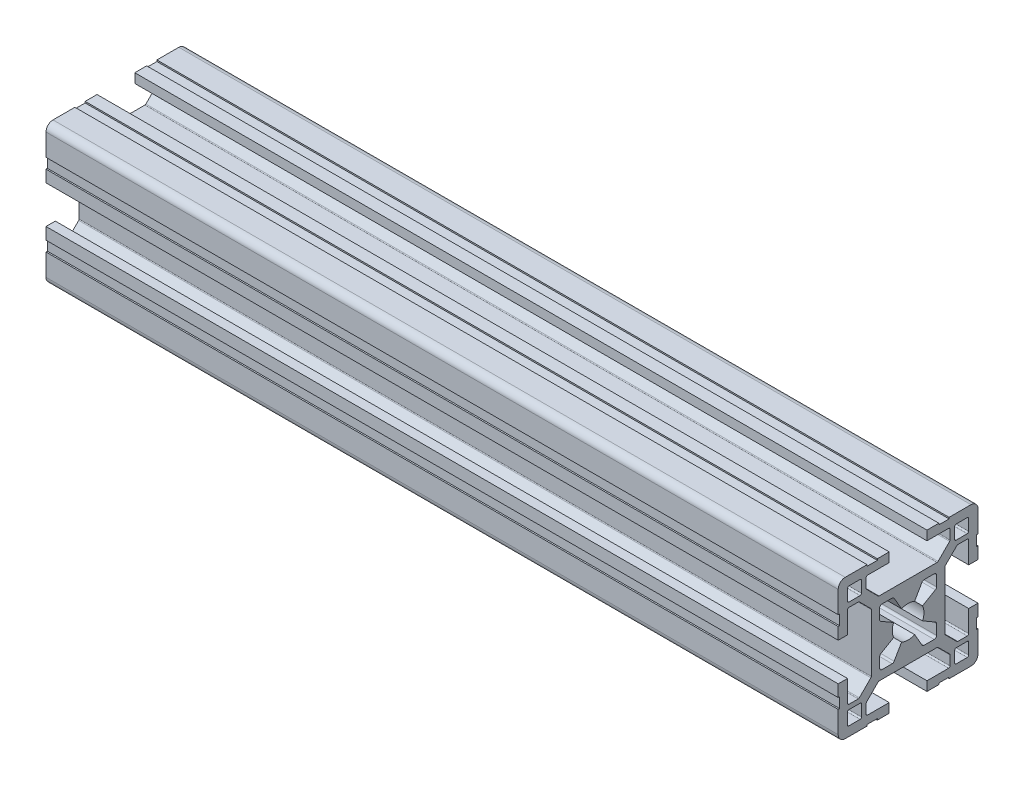
SolidWorks part; units mm, degrees
material "6063-T5"
ref_plane "Plano frontal" through (0, 0, 0) normal (0, 0, 1) x (1, 0, 0)
ref_plane "Plano superior" through (0, 0, 0) normal (0, 1, 0) x (1, 0, 0)
ref_plane "Plano direito" through (0, 0, 0) normal (1, 0, 0) x (0, 0, -1)
sketch "Esboço1" plane through (0, 0, 0) normal (0, 0, 1) x (1, 0, 0)
  line L0 (0, 0) -> (170, 0)
  dimension "D1" = 170
other "Quadrado PF30-11 - PERFIL 3030 CENTRO M8(1)"
ref_plane "Plano1" through (0, 0, 0) normal (1, 0, 0) x (0, 1, 0)
sketch "Sketch1" plane through (0, 0, 0) normal (1, 0, 0) x (0, 1, 0)
  line L0 (-6.1, -3.4254) -> (-6.1, -5.6)
  line L1 (-5.6, -6.1) -> (-3.4254, -6.1)
  line L2 (3.4254, -6.1) -> (5.6, -6.1)
  line L3 (6.1, -5.6) -> (6.1, -3.4254)
  line L4 (6.1, 3.4254) -> (6.1, 5.6)
  line L5 (5.6, 6.1) -> (3.4254, 6.1)
  line L6 (-3.4254, 6.1) -> (-5.6, 6.1)
  line L7 (-6.1, 5.6) -> (-6.1, 3.4254)
  line L8 (15, 6.6) -> (14.7, 6.6)
  line L9 (5.85, -2.9924) -> (3.097, -1.403)
  line L10 (10, 12.7) -> (10, 10.3)
  line L11 (13, -12.7) -> (13, -10.3)
  line L12 (-10.3, -10) -> (-12.7, -10)
  line L13 (-13, 12.7) -> (-13, 10.3)
  line L14 (3.097, 1.403) -> (5.85, 2.9924)
  line L15 (2.9924, 5.85) -> (1.403, 3.097)
  line L16 (-1.403, 3.097) -> (-2.9924, 5.85)
  line L17 (-5.85, 2.9924) -> (-3.097, 1.403)
  line L18 (-3.097, -1.403) -> (-5.85, -2.9924)
  line L19 (-2.9924, -5.85) -> (-1.403, -3.097)
  line L20 (1.403, -3.097) -> (2.9924, -5.85)
  line L21 (10.3, 10) -> (12.7, 10)
  line L22 (13, 10.3) -> (13, 12.7)
  line L23 (12.7, 13) -> (10.3, 13)
  line L24 (12.7, -10) -> (10.3, -10)
  line L25 (10, -10.3) -> (10, -12.7)
  line L26 (10.3, -13) -> (12.7, -13)
  line L27 (-13, -10.3) -> (-13, -12.7)
  line L28 (-12.7, -13) -> (-10.3, -13)
  line L29 (-10, -12.7) -> (-10, -10.3)
  line L30 (-12.7, 10) -> (-10.3, 10)
  line L31 (-10, 10.3) -> (-10, 12.7)
  line L32 (-10.3, 13) -> (-12.7, 13)
  line L33 (15, 4.05) -> (15, 6.6)
  line L34 (13, 4.05) -> (15, 4.05)
  line L35 (13, 8.7) -> (13, 4.05)
  line L36 (10.6799, 9) -> (12.7, 9)
  line L37 (7.9879, 6.4322) -> (10.4678, 8.9121)
  line L38 (7.9, -6.2201) -> (7.9, 6.2201)
  line L39 (10.4678, -8.9121) -> (7.9879, -6.4322)
  line L40 (12.7, -9) -> (10.6799, -9)
  line L41 (13, -4.05) -> (13, -8.7)
  line L42 (15, -4.05) -> (13, -4.05)
  line L43 (15, -6.6) -> (15, -4.05)
  line L44 (14.7, -6.6) -> (15, -6.6)
  line L45 (14.7, -8.8) -> (14.7, -6.6)
  line L46 (15, -8.8) -> (14.7, -8.8)
  line L47 (15, -13.5) -> (15, -8.8)
  line L48 (8.8, -15) -> (13.5, -15)
  line L49 (8.8, -14.7) -> (8.8, -15)
  line L50 (6.6, -14.7) -> (8.8, -14.7)
  line L51 (6.6, -15) -> (6.6, -14.7)
  line L52 (4.05, -15) -> (6.6, -15)
  line L53 (4.05, -13) -> (4.05, -15)
  line L54 (8.7, -13) -> (4.05, -13)
  line L55 (9, -10.6799) -> (9, -12.7)
  line L56 (6.4322, -7.9879) -> (8.9121, -10.4678)
  line L57 (-6.2201, -7.9) -> (6.2201, -7.9)
  line L58 (-8.9121, -10.4678) -> (-6.4322, -7.9879)
  line L59 (-9, -12.7) -> (-9, -10.6799)
  line L60 (-4.05, -13) -> (-8.7, -13)
  line L61 (-4.05, -15) -> (-4.05, -13)
  line L62 (-6.6, -15) -> (-4.05, -15)
  line L63 (-6.6, -14.7) -> (-6.6, -15)
  line L64 (-8.8, -14.7) -> (-6.6, -14.7)
  line L65 (-8.8, -15) -> (-8.8, -14.7)
  line L66 (-13.5, -15) -> (-8.8, -15)
  line L67 (-15, -8.8) -> (-15, -13.5)
  line L68 (-14.7, -8.8) -> (-15, -8.8)
  line L69 (-14.7, -6.6) -> (-14.7, -8.8)
  line L70 (-15, -6.6) -> (-14.7, -6.6)
  line L71 (-15, -4.05) -> (-15, -6.6)
  line L72 (-13, -4.05) -> (-15, -4.05)
  line L73 (-13, -8.7) -> (-13, -4.05)
  line L74 (-10.6799, -9) -> (-12.7, -9)
  line L75 (-7.9879, -6.4322) -> (-10.4678, -8.9121)
  line L76 (-7.9, 6.2201) -> (-7.9, -6.2201)
  line L77 (-10.4678, 8.9121) -> (-7.9879, 6.4322)
  line L78 (-12.7, 9) -> (-10.6799, 9)
  line L79 (-13, 4.05) -> (-13, 8.7)
  line L80 (-15, 4.05) -> (-13, 4.05)
  line L81 (-15, 6.6) -> (-15, 4.05)
  line L82 (-14.7, 6.6) -> (-15, 6.6)
  line L83 (-14.7, 8.8) -> (-14.7, 6.6)
  line L84 (-15, 8.8) -> (-14.7, 8.8)
  line L85 (-15, 13.5) -> (-15, 8.8)
  line L86 (-8.8, 15) -> (-13.5, 15)
  line L87 (-8.8, 14.7) -> (-8.8, 15)
  line L88 (-6.6, 14.7) -> (-8.8, 14.7)
  line L89 (-6.6, 15) -> (-6.6, 14.7)
  line L90 (-4.05, 15) -> (-6.6, 15)
  line L91 (-4.05, 13) -> (-4.05, 15)
  line L92 (-8.7, 13) -> (-4.05, 13)
  line L93 (-9, 10.6799) -> (-9, 12.7)
  line L94 (-6.4322, 7.9879) -> (-8.9121, 10.4678)
  line L95 (6.2201, 7.9) -> (-6.2201, 7.9)
  line L96 (8.9121, 10.4678) -> (6.4322, 7.9879)
  line L97 (9, 12.7) -> (9, 10.6799)
  line L98 (4.05, 13) -> (8.7, 13)
  line L99 (4.05, 15) -> (4.05, 13)
  line L100 (6.6, 15) -> (4.05, 15)
  line L101 (6.6, 14.7) -> (6.6, 15)
  line L102 (8.8, 14.7) -> (6.6, 14.7)
  line L103 (8.8, 15) -> (8.8, 14.7)
  line L104 (13.5, 15) -> (8.8, 15)
  line L105 (15, 8.8) -> (15, 13.5)
  line L106 (14.7, 8.8) -> (15, 8.8)
  line L107 (14.7, 6.6) -> (14.7, 8.8)
  arc A0 (-5.85, -2.9924) -> (-6.1, -3.4254) centre (-5.6, -3.4254) ccw
  arc A1 (-6.1, -5.6) -> (-5.6, -6.1) centre (-5.6, -5.6) ccw
  arc A2 (-3.4254, -6.1) -> (-2.9924, -5.85) centre (-3.4254, -5.6) ccw
  arc A3 (2.9924, -5.85) -> (3.4254, -6.1) centre (3.4254, -5.6) ccw
  arc A4 (5.6, -6.1) -> (6.1, -5.6) centre (5.6, -5.6) ccw
  arc A5 (6.1, -3.4254) -> (5.85, -2.9924) centre (5.6, -3.4254) ccw
  arc A6 (5.85, 2.9924) -> (6.1, 3.4254) centre (5.6, 3.4254) ccw
  arc A7 (6.1, 5.6) -> (5.6, 6.1) centre (5.6, 5.6) ccw
  arc A8 (3.4254, 6.1) -> (2.9924, 5.85) centre (3.4254, 5.6) ccw
  arc A9 (-2.9924, 5.85) -> (-3.4254, 6.1) centre (-3.4254, 5.6) ccw
  arc A10 (-5.6, 6.1) -> (-6.1, 5.6) centre (-5.6, 5.6) ccw
  arc A11 (-6.1, 3.4254) -> (-5.85, 2.9924) centre (-5.6, 3.4254) ccw
  arc A12 (3.097, -1.403) -> (3.097, 1.403) centre (0, 0) ccw
  arc A13 (1.403, 3.097) -> (-1.403, 3.097) centre (0, 0) ccw
  arc A14 (-3.097, 1.403) -> (-3.097, -1.403) centre (0, 0) ccw
  arc A15 (-1.403, -3.097) -> (1.403, -3.097) centre (0, 0) ccw
  arc A16 (10, 10.3) -> (10.3, 10) centre (10.3, 10.3) ccw
  arc A17 (12.7, 10) -> (13, 10.3) centre (12.7, 10.3) ccw
  arc A18 (13, 12.7) -> (12.7, 13) centre (12.7, 12.7) ccw
  arc A19 (10.3, 13) -> (10, 12.7) centre (10.3, 12.7) ccw
  arc A20 (13, -10.3) -> (12.7, -10) centre (12.7, -10.3) ccw
  arc A21 (10.3, -10) -> (10, -10.3) centre (10.3, -10.3) ccw
  arc A22 (10, -12.7) -> (10.3, -13) centre (10.3, -12.7) ccw
  arc A23 (12.7, -13) -> (13, -12.7) centre (12.7, -12.7) ccw
  arc A24 (-12.7, -10) -> (-13, -10.3) centre (-12.7, -10.3) ccw
  arc A25 (-13, -12.7) -> (-12.7, -13) centre (-12.7, -12.7) ccw
  arc A26 (-10.3, -13) -> (-10, -12.7) centre (-10.3, -12.7) ccw
  arc A27 (-10, -10.3) -> (-10.3, -10) centre (-10.3, -10.3) ccw
  arc A28 (-13, 10.3) -> (-12.7, 10) centre (-12.7, 10.3) ccw
  arc A29 (-10.3, 10) -> (-10, 10.3) centre (-10.3, 10.3) ccw
  arc A30 (-10, 12.7) -> (-10.3, 13) centre (-10.3, 12.7) ccw
  arc A31 (-12.7, 13) -> (-13, 12.7) centre (-12.7, 12.7) ccw
  arc A32 (13, 8.7) -> (12.7, 9) centre (12.7, 8.7) ccw
  arc A33 (10.6799, 9) -> (10.4678, 8.9121) centre (10.6799, 8.7) ccw
  arc A34 (7.9879, 6.4322) -> (7.9, 6.2201) centre (8.2, 6.2201) ccw
  arc A35 (7.9, -6.2201) -> (7.9879, -6.4322) centre (8.2, -6.2201) ccw
  arc A36 (10.4678, -8.9121) -> (10.6799, -9) centre (10.6799, -8.7) ccw
  arc A37 (12.7, -9) -> (13, -8.7) centre (12.7, -8.7) ccw
  arc A38 (13.5, -15) -> (15, -13.5) centre (13.5, -13.5) ccw
  arc A39 (8.7, -13) -> (9, -12.7) centre (8.7, -12.7) ccw
  arc A40 (9, -10.6799) -> (8.9121, -10.4678) centre (8.7, -10.6799) ccw
  arc A41 (6.4322, -7.9879) -> (6.2201, -7.9) centre (6.2201, -8.2) ccw
  arc A42 (-6.2201, -7.9) -> (-6.4322, -7.9879) centre (-6.2201, -8.2) ccw
  arc A43 (-8.9121, -10.4678) -> (-9, -10.6799) centre (-8.7, -10.6799) ccw
  arc A44 (-9, -12.7) -> (-8.7, -13) centre (-8.7, -12.7) ccw
  arc A45 (-15, -13.5) -> (-13.5, -15) centre (-13.5, -13.5) ccw
  arc A46 (-13, -8.7) -> (-12.7, -9) centre (-12.7, -8.7) ccw
  arc A47 (-10.6799, -9) -> (-10.4678, -8.9121) centre (-10.6799, -8.7) ccw
  arc A48 (-7.9879, -6.4322) -> (-7.9, -6.2201) centre (-8.2, -6.2201) ccw
  arc A49 (-7.9, 6.2201) -> (-7.9879, 6.4322) centre (-8.2, 6.2201) ccw
  arc A50 (-10.4678, 8.9121) -> (-10.6799, 9) centre (-10.6799, 8.7) ccw
  arc A51 (-12.7, 9) -> (-13, 8.7) centre (-12.7, 8.7) ccw
  arc A52 (-13.5, 15) -> (-15, 13.5) centre (-13.5, 13.5) ccw
  arc A53 (-8.7, 13) -> (-9, 12.7) centre (-8.7, 12.7) ccw
  arc A54 (-9, 10.6799) -> (-8.9121, 10.4678) centre (-8.7, 10.6799) ccw
  arc A55 (-6.4322, 7.9879) -> (-6.2201, 7.9) centre (-6.2201, 8.2) ccw
  arc A56 (6.2201, 7.9) -> (6.4322, 7.9879) centre (6.2201, 8.2) ccw
  arc A57 (8.9121, 10.4678) -> (9, 10.6799) centre (8.7, 10.6799) ccw
  arc A58 (9, 12.7) -> (8.7, 13) centre (8.7, 12.7) ccw
  arc A59 (15, 13.5) -> (13.5, 15) centre (13.5, 13.5) ccw
  point P1 (0, 0)
  point P2 (0, 0)
  point P3 (-15, -15)
  point P4 (0, -15)
  point P5 (-15, 0)
  point P230 (-15, 15)
  point P231 (0, 15)
  point P232 (15, 15)
  point P233 (15, 0)
  point P234 (15, -15)
  point P235 (0, -15)
  point P236 (-15, -15)
  point P237 (-15, 0)
  point P238 (0, 0)
  point P239 (0, 0)
